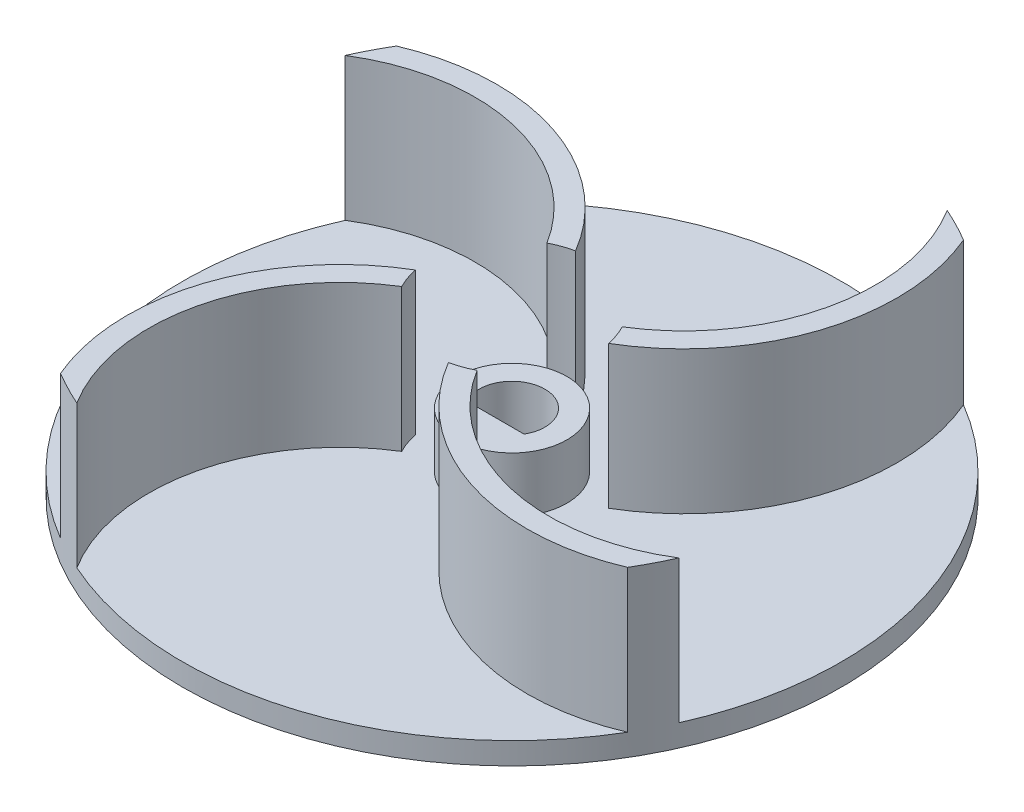
SolidWorks part; units mm, degrees
ref_plane "Front Plane" through (0, 0, 0) normal (0, 0, 1) x (1, 0, 0)
ref_plane "Top Plane" through (0, 0, 0) normal (0, 1, 0) x (1, 0, 0)
ref_plane "Right Plane" through (0, 0, 0) normal (1, 0, 0) x (0, 0, -1)
sketch "Sketch1" plane through (0, 0, 0) normal (0, 1, 0) x (1, 0, 0)
  circle A0 centre (0, 0) radius 30
  dimension "D1" = 60
extrude "Boss-Extrude1" add sketch "Sketch1" along normal blind 2
sketch "Sketch2" plane through (0, 0, 0) normal (0, 1, 0) x (1, 0, 0)
  circle A0 centre (0, 0) radius 5
  dimension "D1" = 10
extrude "Boss-Extrude2" add sketch "Sketch2" along normal blind 7
sketch "Sketch3" plane through (0, 2, 0) normal (0, 1, 0) x (1, 0, 0)
  circle A0 centre (0, 0) radius 7.4461
  circle A1 centre (0, 0) radius 30
  arc A2 (0, 0) -> (-34.3356, 6.2987) centre (-18.2133, -2.5499) ccw
  arc A3 (0.9903, 0.1386) -> (-35.2122, 6.7798) centre (-18.2133, -2.5499) ccw
  arc A4 (-0.9903, -0.1386) -> (-33.4589, 5.8175) centre (-18.2133, -2.5499) ccw
  circle M2 centre (0, 0) radius 5
  circle M3 centre (0, 0) radius 30
  dimension "D1" = 1
  dimension "D2" = 1
extrude "Boss-Extrude3" add sketch "Sketch3" along normal blind 13 contours A4 A2 M2 M3 | A3 A1 A2 M2
sketch "Sketch4" plane through (0, 0, 0) normal (0, 1, 0) x (1, 0, 0)
  line L0 (-2.5981, -1.5) -> (2.5981, -1.5)
  arc A0 (2.5981, -1.5) -> (-2.5981, -1.5) centre (0, 0) ccw
  dimension "D1" = 6
  dimension "D2" = 1.5
extrude "Cut-Extrude1" cut sketch "Sketch4" along normal through all
pattern_circular "CirPattern2" count 4 over 360 about axis through (0, 0, 0) along (0, 1, 0) of "Boss-Extrude3"
